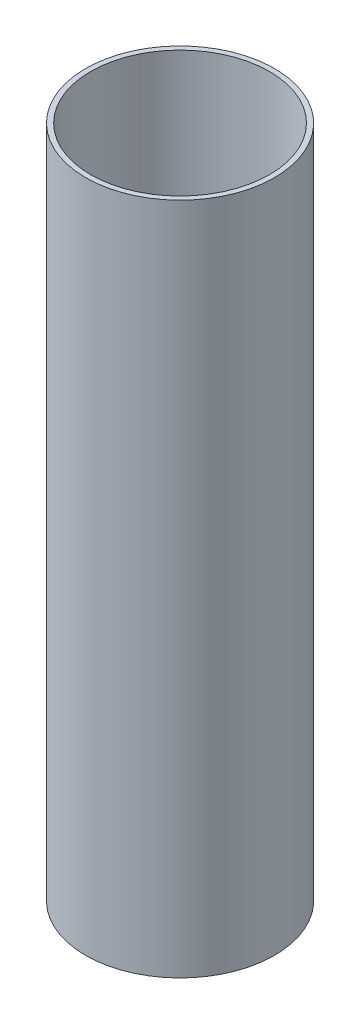
SolidWorks part; units mm, degrees
ref_plane "Front Plane" through (0, 0, 0) normal (0, 0, 1) x (1, 0, 0)
ref_plane "Top Plane" through (0, 0, 0) normal (0, 1, 0) x (1, 0, 0)
ref_plane "Right Plane" through (0, 0, 0) normal (1, 0, 0) x (0, 0, -1)
sketch "Sketch1" plane through (0, 0, 0) normal (0, 0, 1) x (1, 0, 0)
  line L1 (26.9748, 203.2) -> (28.4988, 203.2)
  line L2 (26.9748, 203.2) -> (26.9748, 0)
  line L3 (26.9748, 0) -> (28.4988, 0)
  line L4 (28.4988, 203.2) -> (28.4988, 0)
  dimension "D1" = 0
  dimension "D2" = 26.9748
  dimension "D3" = 1.524
  dimension "D4" = 203.2
ref_axis "Central Axis" through (0, 307.012, 0) along (0, -1, 0)
revolve "Revolve1" add sketch "Sketch1" angle 360 about axis through (0, 307.012, 0) along (0, -1, 0)
